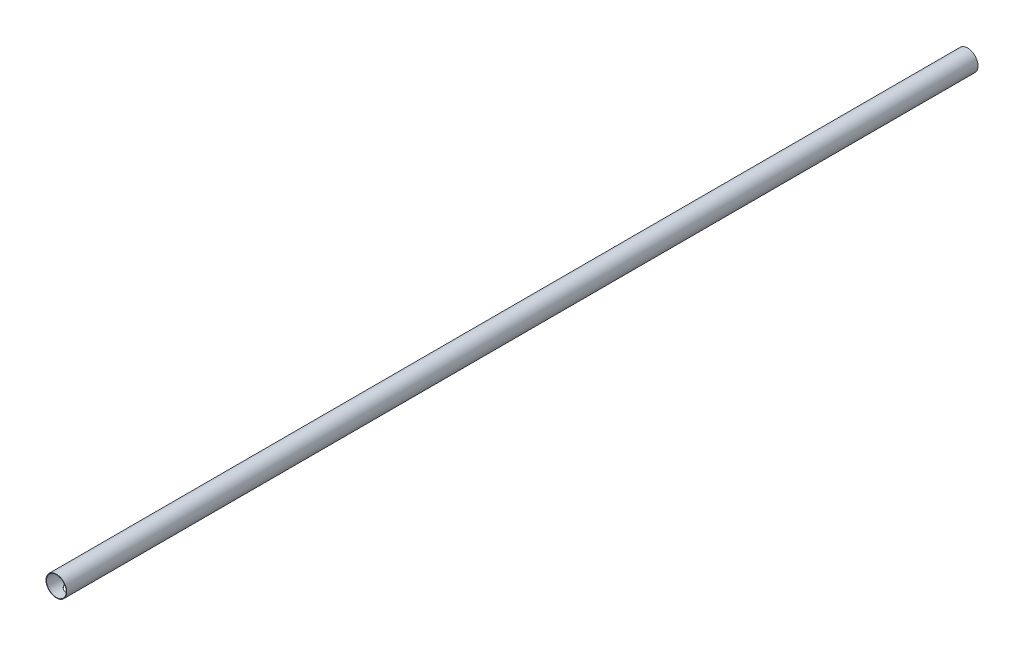
SolidWorks part; units mm, degrees
ref_plane "Front Plane" through (0, 0, 0) normal (0, 0, 1) x (1, 0, 0)
ref_plane "Top Plane" through (0, 0, 0) normal (0, 1, 0) x (1, 0, 0)
ref_plane "Right Plane" through (0, 0, 0) normal (1, 0, 0) x (0, 0, -1)
sketch "Sketch1" plane through (0, 0, 0) normal (0, 0, 1) x (1, 0, 0)
  circle A0 centre (0, 0) radius 56.2121
  circle A1 centre (0, 0) radius 59.2121
  dimension "D2" = 112.4242
  dimension "D1" = 3
extrude "Boss-Extrude1" add sketch "Sketch1" along normal blind 5200
sketch "Sketch3" plane through (0, 0, 0) normal (0, 1, 0) x (1, 0, 0)
  circle A0 centre (0, -5114.6639) radius 32.7203
extrude "Cut-Extrude1" cut sketch "Sketch3" against normal blind 100 contours A0
pattern_linear "LPattern1" count 45 spacing 112.42 along (0, 0, -1) of "Cut-Extrude1"
